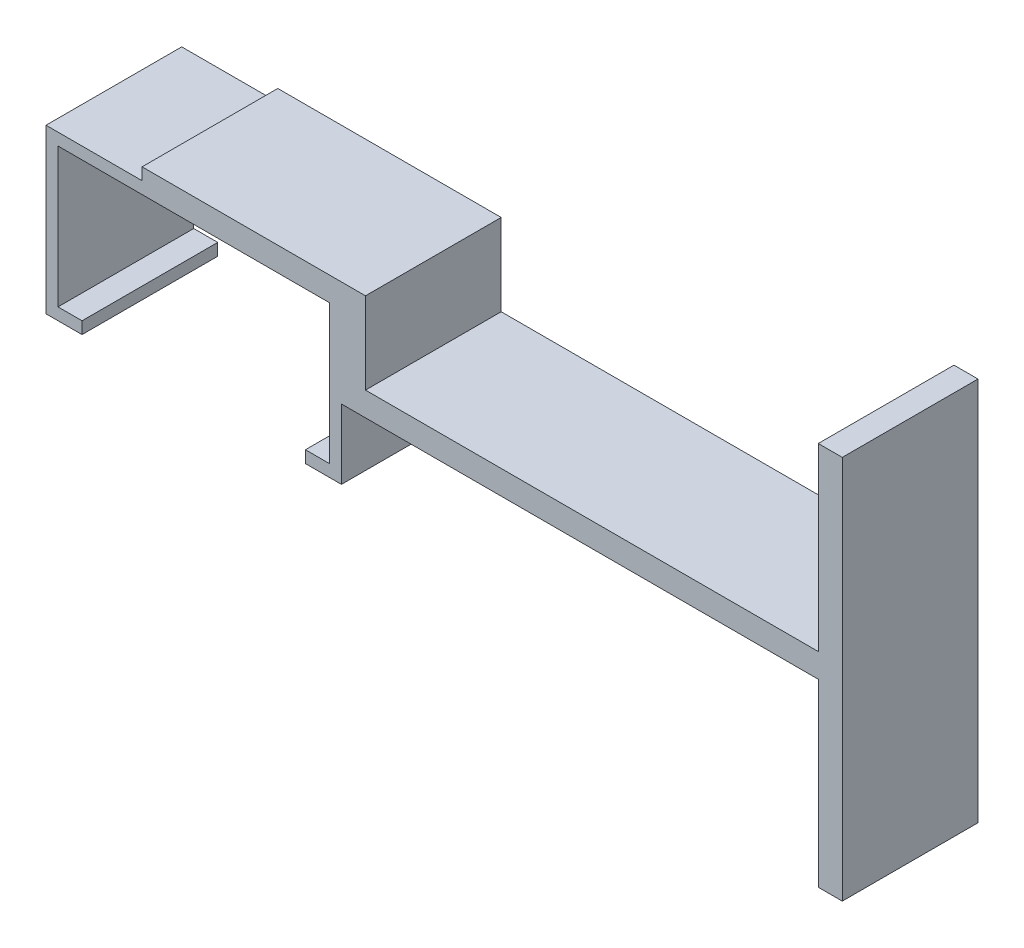
SolidWorks part; units mm, degrees
ref_plane "Plan de face" through (0, 0, 0) normal (0, 0, 1) x (1, 0, 0)
ref_plane "Plan de dessus" through (0, 0, 0) normal (0, 1, 0) x (1, 0, 0)
ref_plane "Plan de droite" through (0, 0, 0) normal (1, 0, 0) x (0, 0, -1)
sketch "Esquisse1" plane through (0, 0, 0) normal (0, 0, 1) x (1, 0, 0)
  line L0 (-21.6, 1) -> (-21.6, 0)
  line L1 (0, 0) -> (-3, 0)
  line L2 (0, 0) -> (0, 13.6)
  line L3 (0, 13.6) -> (-24.6, 13.6)
  line L4 (-24.6, 0) -> (-24.6, 13.6)
  line L5 (-23.6, 12.6) -> (-1, 12.6)
  line L6 (-23.6, 12.6) -> (-23.6, 1)
  line L7 (-23.6, 1) -> (-21.6, 1)
  line L8 (-1, 12.6) -> (-1, 1)
  line L9 (-3, 1) -> (-3, 0)
  line L10 (-3, 1) -> (-1, 1)
  line L11 (-21.6, 0) -> (-24.6, 0)
  dimension "D1" = 13.6
  dimension "D2" = 24.6
  dimension "D3" = 1
  dimension "D4" = 1
  dimension "D5" = 1
  dimension "D6" = 1
  dimension "D7" = 3
  dimension "D8" = 3
extrude "Boss.-Extru.1" add sketch "Esquisse1" along normal blind 11.3
sketch "Esquisse2" plane through (0, 13.6, 0) normal (0, 1, 0) x (1, 0, 0)
  line L0 (0, -11.3) -> (-24.6, -11.3) construction
  line L1 (-16.6, 0) -> (-8, 0)
  line L2 (-16.6, 0) -> (-16.6, -11.3)
  line L3 (-16.6, -11.3) -> (-8, -11.3)
  line L4 (-8, 0) -> (-8, -11.3)
  line L5 (-24.6, -11.3) -> (-24.6, 0) construction
  line L6 (0, -11.3) -> (0, 0) construction
  dimension "D1" = 8
  dimension "D2" = 8
  dimension "D3" = 11.3
extrude "Boss.-Extru.2" add sketch "Esquisse2" along normal blind 1
sketch "Esquisse3" plane through (0, 0, 11.3) normal (0, 0, 1) x (1, 0, 0)
  line L0 (-8, 14.6) -> (-8, 13.6) construction
  line L1 (-16.6, 14.6) -> (-8, 14.6)
  line L2 (-16.6, 14.6) -> (-16.6, 12.6)
  line L3 (-16.6, 12.6) -> (-8, 12.6)
  line L4 (-8, 14.6) -> (-8, 12.6)
  line L5 (-23.6, 12.6) -> (-1, 12.6) construction
  dimension "D1" = 0
  dimension "D2" = 0
sketch "Esquisse8" plane through (-8, 0, 0) normal (1, 0, 0) x (0, 0, -1)
  line L1 (-11.3, 13.6) -> (0, 13.6)
  line L2 (-11.3, 13.6) -> (-11.3, 14.6)
  line L3 (-11.3, 14.6) -> (0, 14.6)
  line L4 (0, 13.6) -> (0, 14.6)
  dimension "D1" = 11.3
extrude "Boss.-Extru.5" add sketch "Esquisse8" along normal blind 10
sketch "Esquisse9" plane through (0, 13.6, 0) normal (0, -1, 0) x (1, 0, 0)
  line L1 (2, 11.3) -> (0, 11.3)
  line L2 (2, 11.3) -> (2, 0)
  line L3 (2, 0) -> (0, 0)
  line L4 (0, 11.3) -> (0, 0)
extrude "Boss.-Extru.6" add sketch "Esquisse9" along normal blind 7.8
sketch "Esquisse10" plane through (2, 0, 0) normal (1, 0, 0) x (0, 0, -1)
  line L0 (0, 5.8) -> (0, 0) construction
  line L1 (-11.3, 5.8) -> (0, 5.8)
  line L2 (-11.3, 5.8) -> (-11.3, 7.8)
  line L3 (-11.3, 7.8) -> (0, 7.8)
  line L4 (0, 5.8) -> (0, 7.8)
  dimension "D1" = 2
extrude "Boss.-Extru.7" add sketch "Esquisse10" along normal blind 39.7
sketch "Esquisse11" plane through (0, 5.8, 0) normal (0, -1, 0) x (1, 0, 0)
  line L0 (41.7, 11.3) -> (0, 11.3) construction
  line L1 (41.7, 0) -> (39.7, 0)
  line L2 (41.7, 0) -> (41.7, 11.3)
  line L3 (41.7, 11.3) -> (39.7, 11.3)
  line L4 (39.7, 0) -> (39.7, 11.3)
  dimension "D1" = 2
extrude "Boss.-Extru.8" add sketch "Esquisse11" along normal blind 15
sketch "Esquisse12" plane through (0, 7.8, 0) normal (0, 1, 0) x (1, 0, 0)
  line L0 (41.7, 0) -> (2, 0) construction
  line L1 (41.7, -11.3) -> (39.7, -11.3)
  line L2 (41.7, -11.3) -> (41.7, 0)
  line L3 (41.7, 0) -> (39.7, 0)
  line L4 (39.7, -11.3) -> (39.7, 0)
  dimension "D1" = 2
extrude "Boss.-Extru.9" add sketch "Esquisse12" along normal blind 15
